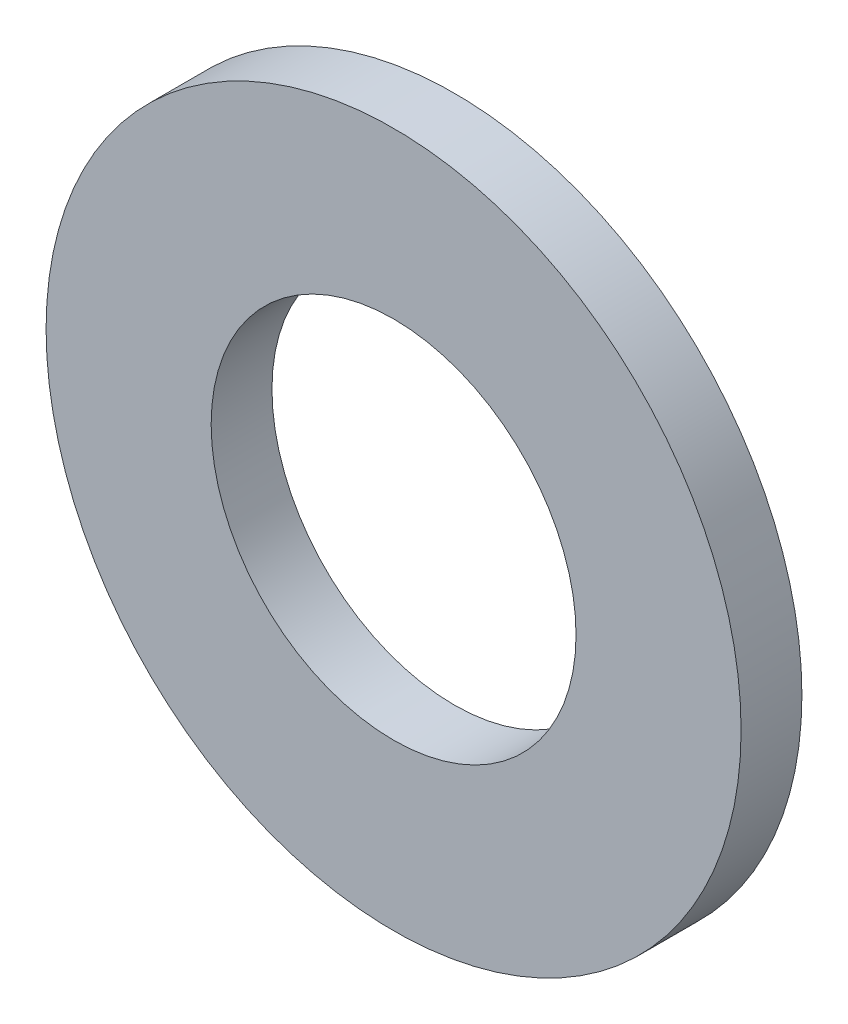
SolidWorks part; units mm, degrees
material "AISI 304"
ref_plane "Front Plane" through (0, 0, 0) normal (0, 0, 1) x (1, 0, 0)
ref_plane "Top Plane" through (0, 0, 0) normal (0, 1, 0) x (1, 0, 0)
ref_plane "Right Plane" through (0, 0, 0) normal (1, 0, 0) x (0, 0, -1)
sketch "Sketch1" plane through (0, 0, 0) normal (0, 0, 1) x (1, 0, 0)
  circle A0 centre (0, 0) radius 4.2
  circle A1 centre (0, 0) radius 8
  dimension "ID" = 8.4
  dimension "OD" = 16
extrude "Extrude1" add sketch "Sketch1" against normal blind 1.4
